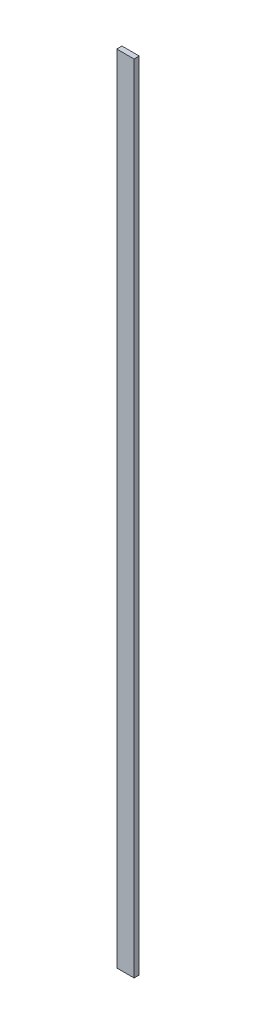
SolidWorks part; units mm, degrees
ref_plane "Plan de face" through (0, 0, 0) normal (0, 0, 1) x (1, 0, 0)
ref_plane "Plan de dessus" through (0, 0, 0) normal (0, 1, 0) x (1, 0, 0)
ref_plane "Plan de droite" through (0, 0, 0) normal (1, 0, 0) x (0, 0, -1)
sketch "Esquisse1" plane through (0, 0, 0) normal (0, 0, 1) x (1, 0, 0)
  line L0 (-33.9085, -447.055) -> (-33.9085, 12.945)
  line L1 (-33.9085, 12.945) -> (-23.9085, 12.945)
  line L3 (-33.9085, -447.055) -> (-23.9085, -447.055)
  line L4 (-23.9085, 12.945) -> (-23.9085, -447.055)
  dimension "D1" = 460
  dimension "D2" = 10
extrude "Boss.-Extru.1" add sketch "Esquisse1" along normal blind 3
equation "\"EpaisseurPlaque\"= 3"
equation "\"D1@Boss.-Extru.1\"=\"EpaisseurPlaque\""
equation "\"ProfondeurBoite\"=460"
equation "\"LongueurSyphon\"=170"
equation "\"LargeurSyphon\"=120"
equation "\"HauteurCoteDroit\"= 490"
equation "\"HauteurCoteGauche\"= 540"
equation "\"HauteurSolSyphon\"= 300"
equation "\"HauteurSyphon\"=\"HauteurCoteGauche\"-\"HauteurSolSyphon\""
equation "\"LargeurDroite\"=10"
equation "\"LargeurGauche\"=150"
equation "\"LargeurBoite\"= \"LargeurDroite\" + \"LargeurGauche\" + \"LargeurSyphon\""
equation "\"D1@Esquisse1\"=\"ProfondeurBoite\""
equation "\"D2@Esquisse1\"=\"LargeurDroite\""
